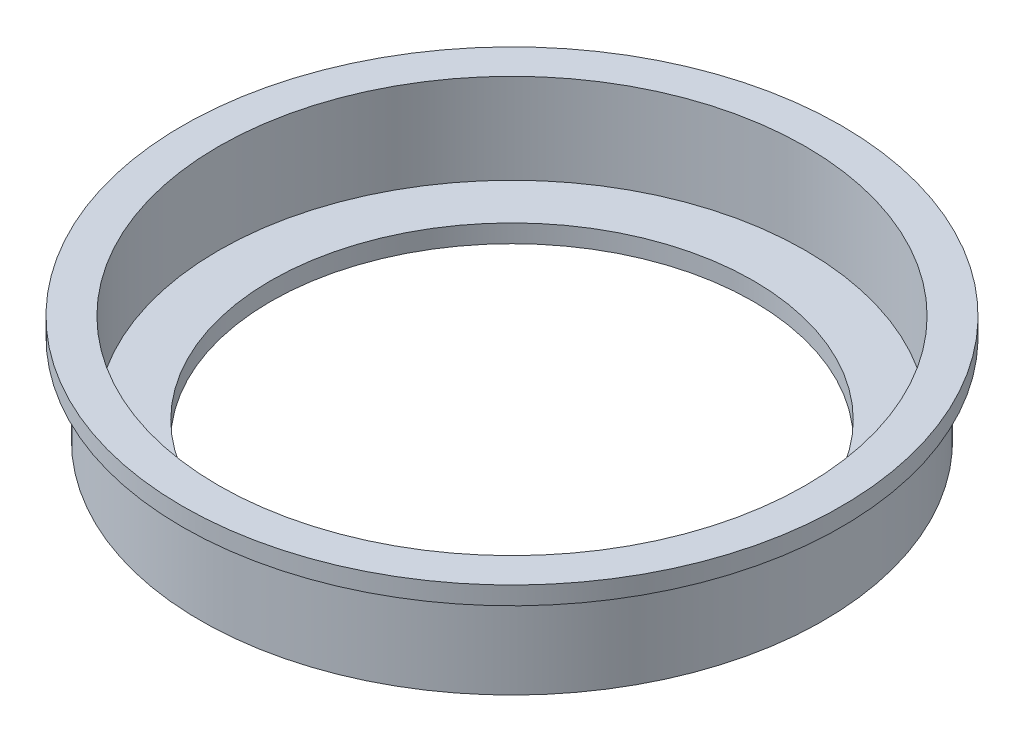
SolidWorks part; units mm, degrees
material "6061-T6 (SS)"
ref_plane "Front Plane" through (0, 0, 0) normal (0, 0, 1) x (1, 0, 0)
ref_plane "Top Plane" through (0, 0, 0) normal (0, 1, 0) x (1, 0, 0)
ref_plane "Right Plane" through (0, 0, 0) normal (1, 0, 0) x (0, 0, -1)
sketch "Sketch1" plane through (0, 0, 0) normal (0, 0, 1) x (1, 0, 0)
  line L0 (0, 0) -> (0, 14.2176) construction
  line L1 (34.036, 0) -> (34.036, 2.54)
  line L2 (34.036, 2.54) -> (41.402, 2.54)
  line L3 (41.402, 2.54) -> (41.402, 15.24)
  line L4 (41.402, 15.24) -> (46.482, 15.24)
  line L5 (46.482, 15.24) -> (46.482, 12.7)
  line L6 (46.482, 12.7) -> (43.942, 12.7)
  line L7 (43.942, 12.7) -> (43.942, 0)
  line L8 (43.942, 0) -> (34.036, 0)
  dimension "D1" = 12.7
  dimension "D2" = 7.366
  dimension "D3" = 5.08
  dimension "D4" = 2.54
  dimension "D5" = 2.54
  dimension "D6" = 82.804
  dimension "D7" = 2.54
revolve "Revolve1" add sketch "Sketch1" angle 360 about L0
equation "\"Aft closure lip axial\"= 0.5"
equation "\"aft closure lip holder\"= .29"
equation "\"Thrust plate connection\"= .2"
equation "\"D1@Sketch1\"=\"Aft closure lip axial\""
equation "\"D2@Sketch1\"=\"aft closure lip holder\""
equation "\"D3@Sketch1\"=\"Thrust plate connection\""
equation "\"retainer lip thickness\"= .1"
equation "\"D4@Sketch1\"=\"retainer lip thickness\""
equation "\"D5@Sketch1\"=\"retainer lip thickness\""
equation "\"Aft closure diameter\"= 3.26"
equation "\"D6@Sketch1\"=\"Aft closure diameter\""
